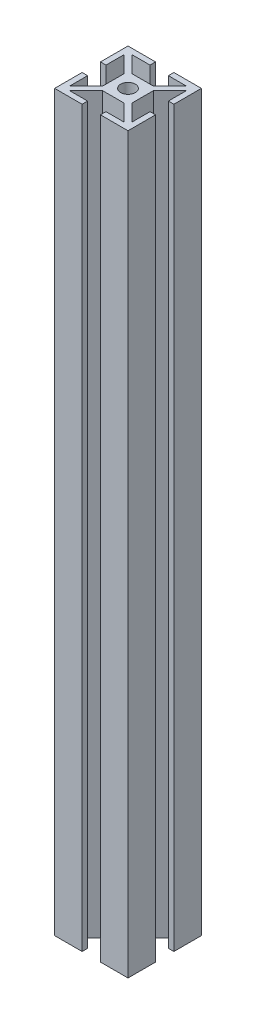
SolidWorks part; units mm, degrees
ref_plane "Płaszczyzna przednia" through (0, 0, 0) normal (0, 0, 1) x (1, 0, 0)
ref_plane "Płaszczyzna górna" through (0, 0, 0) normal (0, 1, 0) x (1, 0, 0)
ref_plane "Płaszczyzna prawa" through (0, 0, 0) normal (1, 0, 0) x (0, 0, -1)
sketch "Szkic1" plane through (0, 0, 0) normal (0, 1, 0) x (1, 0, 0)
  line L0 (-9.4697, -10.5303) -> (10.5303, 9.4697)
  line L1 (-10, -10) -> (10, -10)
  line L2 (-10, -10) -> (-10, 10)
  line L3 (-10, 10) -> (10, 10)
  line L4 (10, -10) -> (10, 10)
  line L5 (-10, -10) -> (10, 10) construction
  line L6 (-10, 10) -> (10, -10) construction
  line L7 (-4, -4) -> (4, -4)
  line L8 (-4, -4) -> (-4, 4)
  line L9 (-4, 4) -> (4, 4)
  line L10 (4, -4) -> (4, 4)
  line L11 (-4, -4) -> (4, 4) construction
  line L12 (-4, 4) -> (4, -4) construction
  line L13 (-9.4697, -10.5303) -> (-10.5303, -9.4697)
  line L14 (10.5303, 9.4697) -> (9.4697, 10.5303)
  line L15 (-10.5303, -9.4697) -> (9.4697, 10.5303)
  line L16 (-9.4697, -10.5303) -> (9.4697, 10.5303) construction
  line L17 (10.5303, 9.4697) -> (-10.5303, -9.4697) construction
  line L22 (-10.5303, 9.4697) -> (9.4697, -10.5303)
  line L23 (-10.5303, 9.4697) -> (-9.4697, 10.5303)
  line L24 (9.4697, -10.5303) -> (10.5303, -9.4697)
  line L25 (-9.4697, 10.5303) -> (10.5303, -9.4697)
  line L26 (-10.5303, 9.4697) -> (10.5303, -9.4697) construction
  line L27 (9.4697, -10.5303) -> (-9.4697, 10.5303) construction
  line L28 (0, 0) -> (0, 10) construction
  line L29 (10, 10) -> (8.5, 10)
  line L30 (10, 10) -> (10, 2.5)
  line L31 (10, 2.5) -> (8.5, 2.5)
  line L32 (8.5, 10) -> (8.5, 2.5)
  line L33 (0, 0) -> (-10, 0) construction
  line L34 (-10, 2.5) -> (-8.5, 2.5)
  line L35 (-8.5, 10) -> (-8.5, 2.5)
  line L36 (-10, 10) -> (-8.5, 10)
  line L37 (-10, 10) -> (-10, 2.5)
  line L38 (-10, -10) -> (-8.5, -10)
  line L39 (-8.5, -10) -> (-8.5, -2.5)
  line L40 (-10, -2.5) -> (-8.5, -2.5)
  line L41 (-10, -10) -> (-10, -2.5)
  line L42 (10, -2.5) -> (8.5, -2.5)
  line L43 (8.5, -10) -> (8.5, -2.5)
  line L44 (10, -10) -> (8.5, -10)
  line L45 (10, -10) -> (10, -2.5)
  line L46 (-10, -10) -> (-10, -8.5)
  line L47 (-10, 8.5) -> (-2.5, 8.5)
  line L48 (-10, 10) -> (-2.5, 10)
  line L49 (-10, -10) -> (-2.5, -10)
  line L50 (2.5, 10) -> (2.5, 8.5)
  line L51 (-2.5, -10) -> (-2.5, -8.5)
  line L52 (-2.5, 10) -> (-2.5, 8.5)
  line L53 (10, 10) -> (2.5, 10)
  line L54 (10, 8.5) -> (2.5, 8.5)
  line L55 (2.5, -10) -> (2.5, -8.5)
  line L56 (10, -10) -> (10, -8.5)
  line L57 (10, -8.5) -> (2.5, -8.5)
  line L58 (10, 10) -> (10, 8.5)
  line L59 (-10, -8.5) -> (-2.5, -8.5)
  line L60 (10, -10) -> (2.5, -10)
  line L61 (-10, 10) -> (-10, 8.5)
  line L62 (-10, -10) -> (10, 10) construction
  line L63 (10, -10) -> (-10, 10) construction
  circle A0 centre (0, 0) radius 2
  point P0 (0, 0)
  point P6 (0, 0)
  point P12 (0, 0)
  point P13 (0, 0)
  point P20 (0, 0)
  dimension "D6" = 4
  dimension "D1" = 20
  dimension "D2" = 20
  dimension "D3" = 8
  dimension "D4" = 1.5
  dimension "D5" = 1.5
  dimension "D7" = 7.5
  dimension "D8" = 1.5
extrude "Dodanie-wyciągnięcie1" add sketch "Szkic1" along normal blind 200 contours L4 L54 L0 L32 L31 | L52 L3 L35 L25 L47 | L35 L3 L25 | L22 L47 L35 L25 L3 L2 | L37 L47 L22 | L47 L2 L34 L35 L22 | L47 L22 L35 | L35 L47 L25 | L47 L35 L22 L8 L9 L25 | L59 L15 L2 L1 L0 L39 | L59 L2 L15 | L41 L59 L15 L39 L40 | L15 L59 L39 | L59 L39 L0 | L1 L39 L0 | L59 L0 L39 L1 L51 | L39 L59 L0 L7 L8 L15 | A0 L15 L9 L25 | A0 L25 L9 L8 L22 | A0 L22 L8 L15 | A0 L15 L8 L7 L0 | A0 L0 L7 L22 | A0 L22 L7 L10 L25 | A0 L25 L10 L0 | A0 L0 L10 L9 L15 | L54 L15 L32 L3 L50 | L54 L32 L15 | L3 L32 L15 | L54 L0 L4 L3 L15 L32 | L0 L54 L32 | L54 L30 L0 | L32 L54 L15 L9 L10 L0 | L57 L43 L25 L10 L7 L22 | L43 L57 L22 | L57 L25 L43 | L57 L45 L42 L43 L25 | L22 L57 L55 L1 L43 | L25 L57 L43 L22 L1 L4 | L43 L1 L22 | L4 L57 L25
